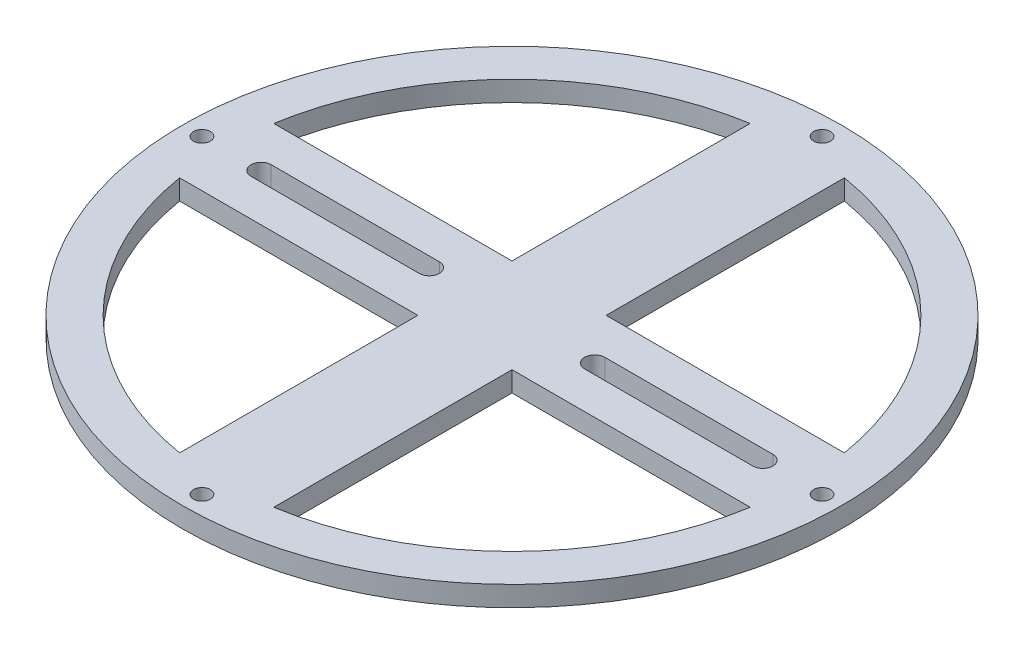
SolidWorks part; units mm, degrees
ref_plane "前视" through (0, 0, 0) normal (0, 0, 1) x (1, 0, 0)
ref_plane "上视" through (0, 0, 0) normal (0, 1, 0) x (1, 0, 0)
ref_plane "右视" through (0, 0, 0) normal (1, 0, 0) x (0, 0, -1)
sketch "草图1" plane through (0, 0, 0) normal (0, 1, 0) x (1, 0, 0)
  line L0 (-66.1799, 0) -> (81.937, 0) construction
  circle A0 centre (0, 0) radius 49
  dimension "D1" = 98
extrude "凸台-拉伸1" add sketch "草图1" along normal blind 3
sketch "草图2" plane through (0, 3, 0) normal (0, 1, 0) x (1, 0, 0)
  line L0 (0, 51.8724) -> (0, -53.4296) construction
  line L1 (-65.7201, 0) -> (62.0667, 0) construction
  circle A1 centre (0, 46.1) radius 1.25
  dimension "D1" = 46.1
  dimension "D2" = 2.5
sketch "草图5" plane through (0, 3, 0) normal (0, 1, 0) x (1, 0, 0)
  line L0 (-59.7985, 0) -> (61.0663, 0) construction
  line L1 (7, -53.9211) -> (7, 55.1109) construction
  line L2 (-63.602, 7) -> (62.9681, 7) construction
  line L4 (7, 42.42) -> (7, 7)
  line L5 (7, 7) -> (42.42, 7)
  arc A0 (7, 42.42) -> (42.42, 7) centre (0, 0) cw
  dimension "D1" = 7
  dimension "D2" = 7
extrude "切除-拉伸3" cut sketch "草图5" against normal through all
sketch "草图6" plane through (0, 3, 0) normal (0, 1, 0) x (1, 0, 0)
  line L0 (-12.3, 0) -> (-37.3, 0) construction
  line L1 (-65.7201, 0) -> (62.0667, 0) construction
  line L2 (-12.3, -1.5) -> (-37.3, -1.5)
  line L3 (-12.3, 1.5) -> (-37.3, 1.5)
  arc A0 (-12.3, -1.5) -> (-12.3, 1.5) centre (-12.3, 0) ccw
  arc A1 (-37.3, 1.5) -> (-37.3, -1.5) centre (-37.3, 0) ccw
  point P4 (-24.8, 0)
  dimension "D1" = 12.3
  dimension "D2" = 25
extrude "切除-拉伸4" cut sketch "草图6" against normal through all
pattern_circular "阵列(圆周)4" count 2 over 360 about axis through (0, 0, 0) along (0, 1, 0) of "切除-拉伸4"
extrude "切除-拉伸5" cut sketch "草图2" against normal through all
pattern_circular "阵列(圆周)5" count 4 over 360 about axis through (0, 0, 0) along (0, 1, 0) of "切除-拉伸5"
sketch "草图7" plane through (0, 3, 0) normal (0, 1, 0) x (1, 0, 0)
  line L0 (24.8, 2.9726) -> (24.8, -3.72) construction
pattern_circular "阵列(圆周)6" count 4 over 360 about axis through (0, 0, 0) along (0, 1, 0) of "切除-拉伸3"
